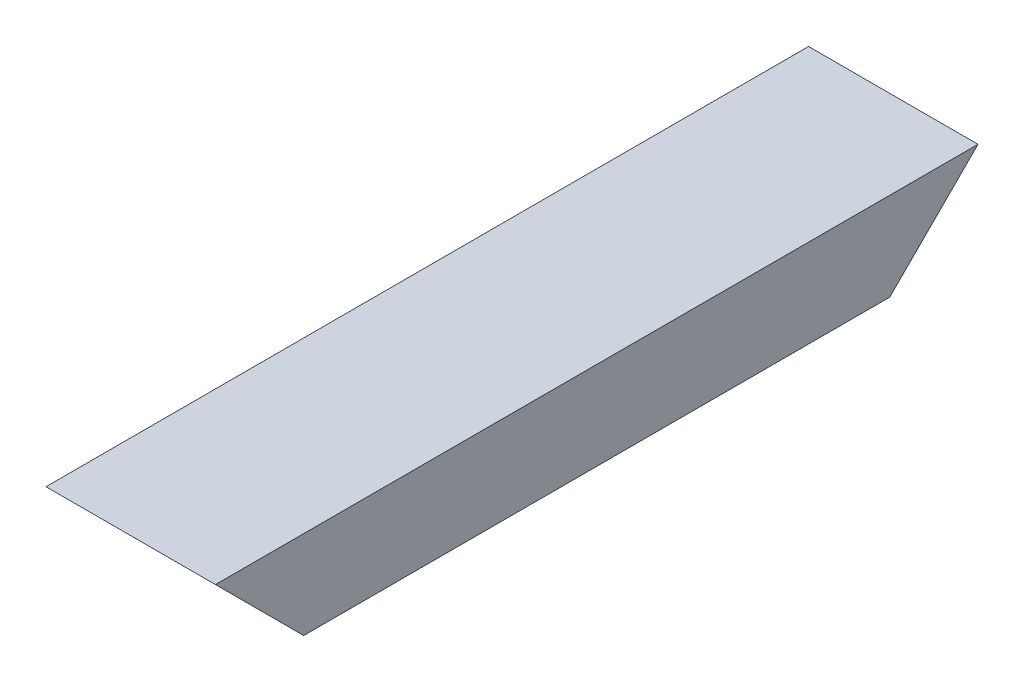
SolidWorks part; units mm, degrees
ref_plane "Plan de face" through (0, 0, 0) normal (0, 0, 1) x (1, 0, 0)
ref_plane "Plan de dessus" through (0, 0, 0) normal (0, 1, 0) x (1, 0, 0)
ref_plane "Plan de droite" through (0, 0, 0) normal (1, 0, 0) x (0, 0, -1)
sketch "Esquisse1" plane through (0, 0, 0) normal (0, 0, 1) x (1, 0, 0)
  line L0 (105.75, 119) -> (105.75, 94)
  line L1 (105.75, 119) -> (105.75, -103) construction
  line L2 (105.75, 94) -> (80.75, 94)
  line L3 (80.75, 94) -> (80.75, 102)
  line L4 (80.75, 102) -> (57.75, 102)
  line L5 (57.75, 102) -> (57.75, 119)
  line L6 (57.75, 119) -> (105.75, 119)
  point P4 (105.75, 119)
  dimension "D1" = 8
  dimension "D2" = 17
  dimension "D3" = 23
  dimension "D4" = 25
extrude "Boss.-Extru.1" add sketch "Esquisse1" along normal up to vertex (216 mm away)
sketch "Esquisse3" plane through (105.75, 0, 0) normal (1, 0, 0) x (0, 0, -1)
  line L0 (0, 119) -> (-25, 94)
  line L1 (-216, 94) -> (0, 94) construction
  line L2 (-25, 94) -> (0, 94)
  line L3 (0, 94) -> (0, 119)
  line L5 (-191, 94) -> (-216, 94)
  line L6 (-216, 94) -> (-216, 119)
  line L7 (-216, 119) -> (-191, 94)
  point P9 (-216, 142.9651)
extrude "Enlèv. mat.-Extru.1" cut sketch "Esquisse3" against normal through all
